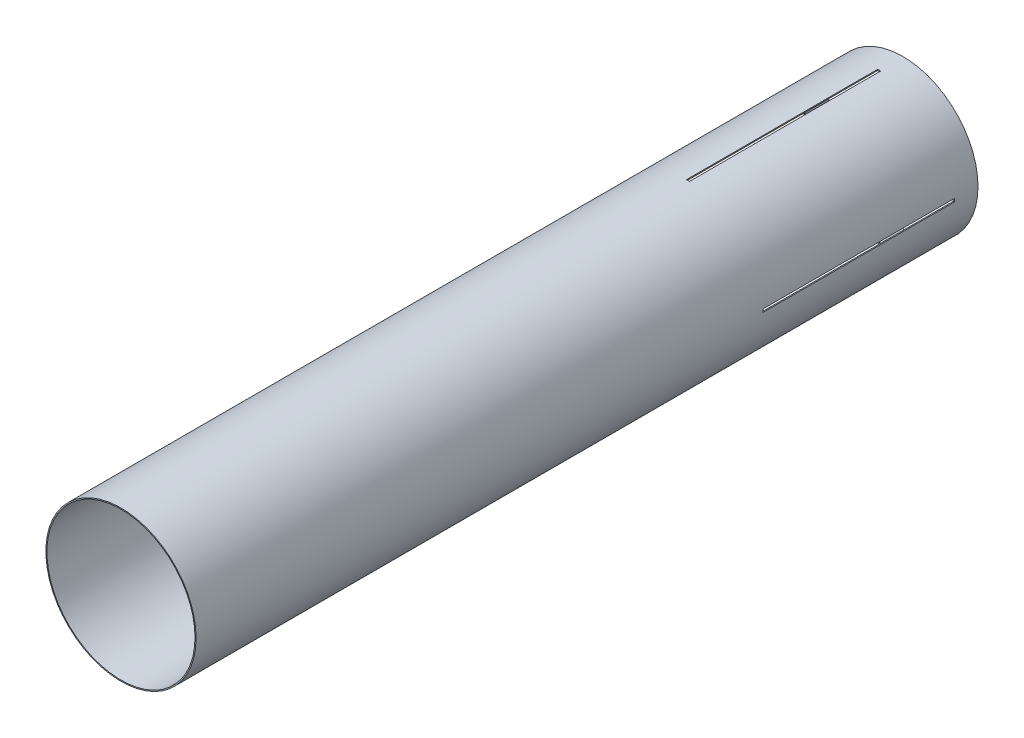
SolidWorks part; units mm, degrees
ref_plane "Front Plane" through (0, 0, 0) normal (0, 0, 1) x (1, 0, 0)
ref_plane "Top Plane" through (0, 0, 0) normal (0, 1, 0) x (1, 0, 0)
ref_plane "Right Plane" through (0, 0, 0) normal (1, 0, 0) x (0, 0, -1)
sketch "Sketch1" plane through (0, 0, 0) normal (0, 0, 1) x (1, 0, 0)
  circle A0 centre (0, 0) radius 79.375
  circle A1 centre (0, 0) radius 80.518
  dimension "D1" = 1.143
  dimension "D2" = 161.036
extrude "Boss-Extrude1" add sketch "Sketch1" along normal blind 838.2
sketch "Sketch2" plane through (0, 0, 0) normal (0, 0, -1) x (-1, 0, 0)
  line L0 (0, 0) -> (0, 80.518) construction
  circle A0 centre (0, 0) radius 80.518 construction
ref_plane "Plane1" through (0, 80.518, 0) normal (0, 1, 0) x (1, 0, 0)
sketch "Sketch3" plane through (0, 80.518, 0) normal (0, 1, 0) x (1, 0, 0)
  line L0 (0, 0) -> (0, -25.4) construction
  line L1 (-1.6002, -25.4) -> (1.6002, -25.4)
  line L2 (-1.6002, -25.4) -> (-1.6002, -230.378)
  line L3 (-1.6002, -230.378) -> (1.6002, -230.378)
  line L4 (1.6002, -25.4) -> (1.6002, -230.378)
  line L5 (79.375, 0) -> (-79.375, 0) construction
  dimension "D1" = 3.2004
  dimension "D2" = 25.4
  dimension "D3" = 204.978
extrude "Cut-Extrude1" cut sketch "Sketch3" against normal up to surface (1.1591 mm away)
pattern_circular "CirPattern1" count 4 over 360 about axis through (0, 0, 0) along (0, 0, 1) of "Cut-Extrude1"
